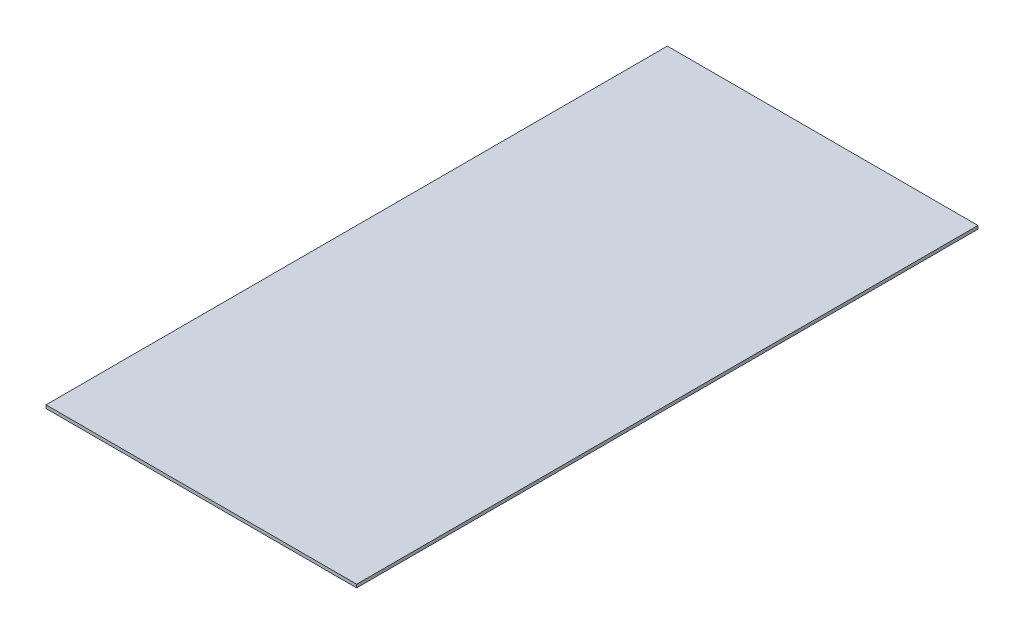
SolidWorks part; units mm, degrees
ref_plane "Front Plane" through (0, 0, 0) normal (0, 0, 1) x (1, 0, 0)
ref_plane "Top Plane" through (0, 0, 0) normal (0, 1, 0) x (1, 0, 0)
ref_plane "Right Plane" through (0, 0, 0) normal (1, 0, 0) x (0, 0, -1)
sketch "Sketch2" plane through (0, 0, 0) normal (0, 1, 0) x (1, 0, 0)
  line L1 (-152.4, 304.8) -> (152.4, 304.8)
  line L2 (-152.4, 304.8) -> (-152.4, -304.8)
  line L3 (-152.4, -304.8) -> (152.4, -304.8)
  line L4 (152.4, 304.8) -> (152.4, -304.8)
  line L5 (-152.4, 304.8) -> (152.4, -304.8) construction
  line L6 (-152.4, -304.8) -> (152.4, 304.8) construction
  point P0 (0, 0)
  dimension "D1" = 609.6
  dimension "D2" = 304.8
extrude "Boss-Extrude1" add sketch "Sketch2" along normal blind 3.175
